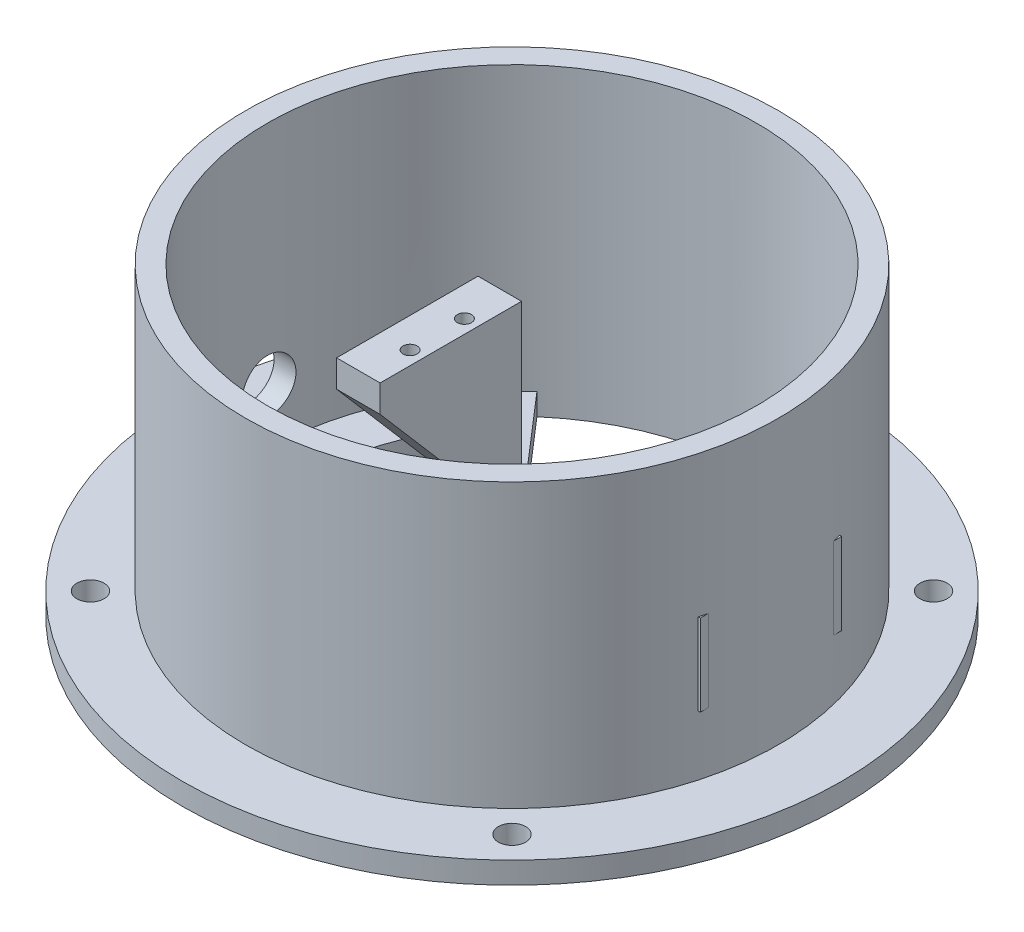
SolidWorks part; units mm, degrees
ref_plane "Ön Düzlem" through (0, 0, 0) normal (0, 0, 1) x (1, 0, 0)
ref_plane "Üst Düzlem" through (0, 0, 0) normal (0, 1, 0) x (1, 0, 0)
ref_plane "Sağ Düzlem" through (0, 0, 0) normal (1, 0, 0) x (0, 0, -1)
sketch "Çizim1" plane through (0, 0, 0) normal (0, 0, 1) x (1, 0, 0)
  line L0 (0, 14.3857) -> (0, -10.3824) construction
  line L1 (0, -34.3103) -> (0, 34.3103) construction
  line L3 (33.3438, 0) -> (-33.3438, 0) construction
  line L7 (60.625, 4) -> (60.625, 0)
  line L8 (45, 0) -> (45, 56)
  line L9 (45, 56) -> (49, 56)
  line L10 (49, 56) -> (49, 4)
  line L12 (45, 0) -> (60.625, 0)
  line L13 (49, 4) -> (60.625, 4)
  line L14 (45, 0) -> (60.625, 0)
  dimension "D1" = 52
  dimension "D2" = 45
  dimension "D5" = 4
  dimension "D7" = 4
revolve "Döndür5" add sketch "Çizim1" angle 360 about L0
ref_plane "Düzlem3" through (45, 0, 0) normal (-1, 0, 0) x (0, 0, 1)
sketch "Çizim7" plane through (45, 0, 0) normal (-1, 0, 0) x (0, 0, 1)
  line L0 (0, 56) -> (0, 38)
  line L1 (45, 56) -> (-45, 56) construction
  line L2 (0, -30.8) -> (0, 30.8) construction
  line L3 (-13, 38) -> (13, 38)
  line L4 (13, 38) -> (13, 30)
  line L5 (13, 30) -> (-13, 30)
  line L6 (-13, 30) -> (-13, 38)
  dimension "D1" = 18
  dimension "D2" = 8
  dimension "D3" = 26
  dimension "D4" = 13
extrude "Yükseklik-Ekstrüzyon3" add sketch "Çizim7" along normal blind 15 contours L6 L5 L4 L3
sketch "Çizim8" plane through (0, 0, 0) normal (0, 1, 0) x (1, 0, 0)
  line L0 (-6.25, 0) -> (-11.25, 0)
  line L1 (-30.8, 0) -> (30.8, 0) construction
  line L2 (-11.25, 13) -> (-11.25, -13)
  line L3 (-11.25, -13) -> (-19.25, -13)
  line L4 (-19.25, -13) -> (-19.25, 13)
  line L5 (-19.25, 13) -> (-11.25, 13)
  line L6 (-11.25, 13) -> (-29.447, 34.0276)
  line L7 (-28.1156, 20.6074) -> (-28.2856, 20.4602)
  line L8 (-29.447, 22.4026) -> (-24.25, 15.3948)
  line L9 (-24.25, -15.8349) -> (-24.25, 15.3948)
  line L10 (-24.25, 18) -> (-6.25, 18) construction
  line L11 (-6.25, 18) -> (-6.25, -18) construction
  line L12 (-6.25, -18) -> (-24.25, -18) construction
  line L13 (-11.25, -13) -> (-29.447, -34.0276)
  line L14 (-29.1815, -21.5335) -> (-29.2004, -21.5173)
  line L15 (-29.6734, -22.1019) -> (-24.25, -15.8349)
  line L16 (-24.25, -18) -> (-24.25, 18) construction
  arc A0 (-29.447, 22.4026) -> (-29.6734, -22.1019) centre (0, 0) ccw
  circle A1 centre (0, 0) radius 45 construction
  arc A2 (-29.447, 34.0276) -> (-29.447, -34.0276) centre (0, 0) ccw
  dimension "D1" = 74
  dimension "D2" = 11.25
  dimension "D6" = 90
  dimension "D3" = 8
  dimension "D4" = 5
extrude "Yükseklik-Ekstrüzyon4" add sketch "Çizim8" along normal blind 4 contours L5 L4 L3 L2 | L6 A2 L13 L3 L4 L5 A0 L8 L9 L15
sketch "Çizim9" plane through (0, 0, 0) normal (0, 1, 0) x (1, 0, 0)
  line L0 (-11.25, -13) -> (-19.25, -13)
  line L1 (-19.25, -13) -> (-19.25, 13)
  line L2 (-19.25, 13) -> (-11.25, 13)
  line L3 (-11.25, 13) -> (-11.25, -13)
  dimension "D1" = 8
extrude "Yükseklik-Ekstrüzyon5" add sketch "Çizim9" along normal blind 38
ref_plane "Düzlem4" through (-19.25, 0, 0) normal (-1, 0, 0) x (0, 0, 1)
sketch "Çizim11" plane through (-19.25, 0, 0) normal (-1, 0, 0) x (0, 0, 1)
  line L1 (0, -30.8) -> (0, 30.8) construction
  circle A0 centre (0, 14) radius 5
  dimension "D2" = 10
extrude "Kes-Ekstrüzyon1" cut sketch "Çizim11" along normal blind 44
sketch "Çizim12" plane through (0, 0, 0) normal (0, 1, 0) x (1, 0, 0)
  circle A2 centre (-38.7565, 38.7565) radius 2.5
  circle A3 centre (38.7565, 38.7565) radius 2.5
  circle A4 centre (-38.7565, -38.7565) radius 2.5
  circle A5 centre (38.7565, -38.7565) radius 2.5
  dimension "D4" = 5
extrude "Kes-Ekstrüzyon2" cut sketch "Çizim12" along normal blind 44
ref_plane "Düzlem5" through (0, 38, 0) normal (0, 1, 0) x (1, 0, 0)
sketch "Çizim14" plane through (0, 38, 0) normal (0, 1, 0) x (1, 0, 0)
  circle A0 centre (-13.75, 5) radius 1.3
  circle A1 centre (-13.75, -5) radius 1.3
  circle A2 centre (34.25, -5) radius 1.3
  circle A3 centre (34.25, 5) radius 1.3
  dimension "D4" = 2.6
  dimension "D5" = 2
  dimension "D1" = 10
  dimension "D2" = 5
extrude "Kes-Ekstrüzyon3" cut sketch "Çizim14" against normal blind 4
sketch "Çizim15" plane through (-19.25, 0, 0) normal (-1, 0, 0) x (0, 0, 1)
  line L3 (13, 30.0721) -> (-5.0721, 12)
  line L4 (13, 38) -> (13, 4) construction
  line L5 (-5.0721, 12) -> (13, 12)
  line L6 (13, 30.0721) -> (13, 12)
extrude "Kes-Ekstrüzyon4" cut sketch "Çizim15" against normal blind 10
ref_plane "Düzlem7" through (0, 0, 13) normal (0, 0, 1) x (1, 0, 0)
sketch "Çizim16" plane through (0, 0, 13) normal (0, 0, 1) x (1, 0, 0)
  line L0 (30, 30) -> (45.4099, 14.5901)
  line L1 (45.4099, 14.5901) -> (45.4099, 30)
  line L2 (45.4099, 30) -> (30, 30)
extrude "Yükseklik-Ekstrüzyon6" add sketch "Çizim16" against normal blind 26
sketch "Çizim17" plane through (0, 0, 0) normal (0, 1, 0) x (1, 0, 0)
  line L0 (0, -45) -> (0, 45)
  arc A0 (0, -45) -> (0, 45) centre (0, 0) ccw
extrude "Kes-Ekstrüzyon5" cut sketch "Çizim17" along normal blind 30
sketch "Çizim18" plane through (0, 0, 13) normal (0, 0, 1) x (1, 0, 0)
  line L0 (30, 30) -> (45, 15)
  line L1 (30, 30) -> (43.0813, 30) construction
  line L2 (45, 30.8) -> (45, -30.8) construction
  line L3 (45, 15) -> (47.6252, 15)
  line L4 (47.6252, 15) -> (47.6252, 30)
  line L5 (47.6252, 30) -> (30, 30)
  line L6 (30, 30) -> (29.9268, 30.1426)
  line M1 (30, 30) -> (43.0813, 30)
extrude "Yükseklik-Ekstrüzyon7" add sketch "Çizim18" against normal blind 26 contours L4 L5 L0 L3 M1
sketch "Çizim19" plane through (0, 0, 13) normal (0, 0, 1) x (1, 0, 0)
  line L0 (30, 30) -> (45, 7.6214)
  line L1 (45, 30.8) -> (45, -30.8) construction
  line L2 (30, 30) -> (46.502, 30)
  line L3 (46.502, 30) -> (46.502, 7.6214)
  line L4 (46.502, 7.6214) -> (45, 7.6214)
extrude "Yükseklik-Ekstrüzyon8" add sketch "Çizim19" against normal blind 26
sketch "Çizim20" plane through (-19.25, 0, 0) normal (-1, 0, 0) x (0, 0, 1)
  line L0 (13, 33) -> (-5.0721, 12)
  line L1 (13, -7.1947) -> (13, 7.1947) construction
  line L2 (4.4, 38) -> (-4.4, 38) construction
  line L3 (-5.0721, 12) -> (13, 12)
  line L4 (13, 12) -> (13, 33)
  dimension "D1" = 5
extrude "Kes-Ekstrüzyon6" cut sketch "Çizim20" against normal blind 26
